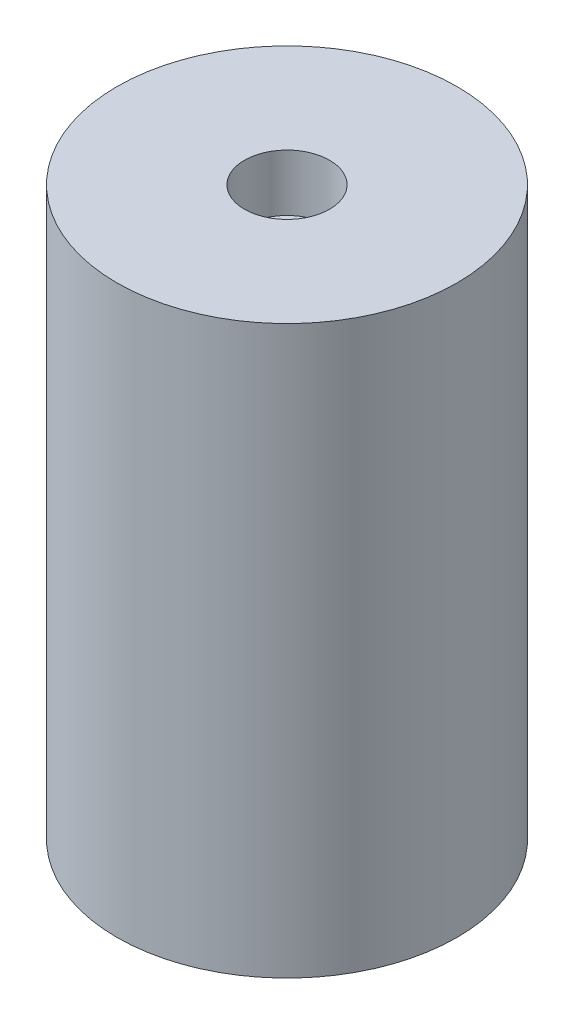
SolidWorks part; units mm, degrees
ref_plane "Front Plane" through (0, 0, 0) normal (0, 0, 1) x (1, 0, 0)
ref_plane "Top Plane" through (0, 0, 0) normal (0, 1, 0) x (1, 0, 0)
ref_plane "Right Plane" through (0, 0, 0) normal (1, 0, 0) x (0, 0, -1)
sketch "Sketch1" plane through (0, 0, 0) normal (0, 1, 0) x (1, 0, 0)
  circle A0 centre (0, 0) radius 6
extrude "Boss-Extrude1" add sketch "Sketch1" along normal blind 20
sketch "Sketch2" plane through (0, 20, 0) normal (0, 1, 0) x (1, 0, 0)
  circle A0 centre (0, 0) radius 1.5
extrude "Cut-Extrude1" cut sketch "Sketch2" against normal blind 2
